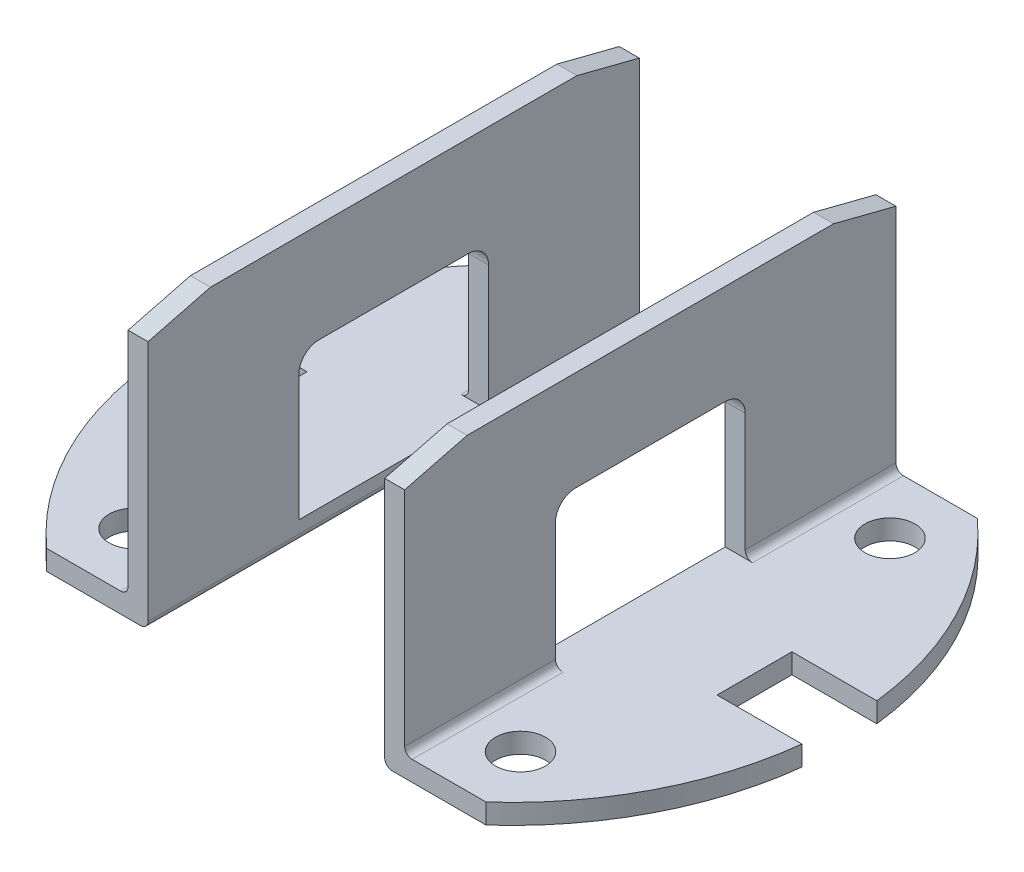
SolidWorks part; units mm, degrees
ref_plane "Front Plane" through (0, 0, 0) normal (0, 0, 1) x (1, 0, 0)
ref_plane "Top Plane" through (0, 0, 0) normal (0, 1, 0) x (1, 0, 0)
ref_plane "Right Plane" through (0, 0, 0) normal (1, 0, 0) x (0, 0, -1)
sketch "Sketch1" plane through (0, 0, 0) normal (0, 1, 0) x (1, 0, 0)
  line L0 (0, 1031.2918) -> (0, -1025.4955) construction
  line L1 (0, 0) -> (-28.6316, 0) construction
  line L2 (11.1742, 12.4968) -> (6.0198, 12.4968)
  line L3 (11.1742, -12.4968) -> (6.0198, -12.4968)
  line L4 (-6.0198, -12.4968) -> (-11.1742, -12.4968)
  line L5 (6.0198, 12.4968) -> (6.0198, -12.4968)
  line L6 (-6.0198, 12.4968) -> (-6.0198, -12.4968)
  line L7 (6.0198, 1031.2918) -> (6.0198, -1025.4955) construction
  line L8 (0, 12.4968) -> (-28.6316, 12.4968) construction
  line L9 (0, -12.4968) -> (-28.6316, -12.4968) construction
  line L10 (-6.0198, 12.4968) -> (-11.1742, 12.4968)
  line L13 (16.6554, 1.905) -> (12.3374, 1.905)
  line L14 (12.3374, 1.905) -> (12.3374, -1.905)
  line L15 (16.6554, -1.905) -> (12.3374, -1.905)
  line L16 (-16.6554, -1.905) -> (-12.3374, -1.905)
  line L18 (-12.3374, 1.905) -> (-12.3374, -1.905)
  line L19 (-16.6554, 1.905) -> (-12.3374, 1.905)
  arc A0 (-11.1742, 12.4968) -> (-16.6554, 1.905) centre (0, 0) ccw
  arc A1 (11.1742, -12.4968) -> (16.6554, -1.905) centre (0, 0) ccw
  arc A2 (-16.6554, -1.905) -> (-11.1742, -12.4968) centre (0, 0) ccw
  arc A4 (16.6554, 1.905) -> (11.1742, 12.4968) centre (0, 0) ccw
  circle A6 centre (-9.8298, 9.398) radius 1.27
  circle A9 centre (-9.8298, -9.398) radius 1.27
  circle A10 centre (9.8298, -9.398) radius 1.27
  circle A11 centre (9.8298, 9.398) radius 1.27
  point P11 (-6.0198, 1031.2918)
  point P12 (-6.0198, -25.4955)
  point P22 (-5.0038, 13.5128)
  point P23 (-5.0038, -13.5128)
  point P24 (-11.5556, -13.5128)
  point P25 (0, 0)
  point P26 (-11.5556, 13.5128)
  point P27 (5.0038, 13.5128)
  point P28 (5.0038, -13.5128)
  point P29 (11.5556, -13.5128)
  point P30 (0, 0)
  point P31 (11.5556, 13.5128)
  point P34 (-10.7792, -11.4808)
  point P35 (0, 0)
  point P36 (-10.7792, 11.4808)
  point P39 (10.7792, -11.4808)
  point P40 (0, 0)
  point P41 (10.7792, 11.4808)
  point P50 (12.3374, 0)
  dimension "D1" = 33.528
  dimension "D8" = 2.54
  dimension "D4" = 1.905
  dimension "D7" = 4.318
  dimension "D9" = 9.398
  dimension "D10" = 3.81
  dimension "D6" = 6.0198
  dimension "D2" = 12.4968
  dimension "D3" = 12.4968
  dimension "D5" = 6.0198
extrude "Boss-Extrude1" add sketch "Sketch1" along normal blind 1.016
sketch "Sketch2" plane through (0, 0, 0) normal (0, 1, 0) x (1, 0, 0)
  line L0 (-6.0198, -12.4968) -> (-6.0198, 12.4968) construction
  line L1 (6.0198, 12.4968) -> (6.0198, -12.4968) construction
  line L2 (-6.0198, -12.4968) -> (-6.0198, 12.4968)
  line L3 (6.0198, 12.4968) -> (6.0198, -12.4968)
  line L4 (-7.0358, -12.4968) -> (-7.0358, 12.4968)
  line L5 (7.0358, 12.4968) -> (7.0358, -12.4968)
  line L6 (-6.0198, 12.4968) -> (-11.1742, 12.4968) construction
  line L7 (-11.1742, -12.4968) -> (-6.0198, -12.4968) construction
  line L8 (6.0198, -12.4968) -> (11.1742, -12.4968) construction
  line L9 (11.1742, 12.4968) -> (6.0198, 12.4968) construction
  line L10 (-6.0198, 12.4968) -> (-7.0358, 12.4968)
  line L11 (-7.0358, -12.4968) -> (-6.0198, -12.4968)
  line L12 (6.0198, -12.4968) -> (7.0358, -12.4968)
  line L13 (7.0358, 12.4968) -> (6.0198, 12.4968)
  dimension "D1" = 1.016
  dimension "D2" = 1.016
extrude "Boss-Extrude2" add sketch "Sketch2" along normal blind 13.5128
sketch "Sketch3" plane through (0, 0, 0) normal (1, 0, 0) x (0, 0, -1)
  line L0 (-12.4968, 13.5128) -> (12.4968, 13.5128) construction
  line L1 (-12.4968, 13.5128) -> (-12.4968, 1.016) construction
  line L2 (12.4968, 13.5128) -> (12.4968, 1.016) construction
  line L3 (-12.4968, 13.5128) -> (-9.3218, 13.5128)
  line L4 (-12.4968, 13.5128) -> (-12.4968, 12.7)
  line L5 (12.4968, 13.5128) -> (12.4968, 12.7)
  line L6 (0, 0) -> (0, 16.3845) construction
  line L7 (9.3218, 13.5128) -> (12.4968, 13.5128)
  line L8 (-9.3218, 13.5128) -> (-12.4968, 12.7)
  line L9 (9.3218, 13.5128) -> (12.4968, 12.7)
  line L10 (-4.826, 7.4168) -> (-4.826, 1.016)
  line L11 (-1.905, 1.016) -> (-12.4968, 1.016) construction
  line L12 (-3.81, 8.4328) -> (3.81, 8.4328)
  line L13 (4.826, 7.4168) -> (4.826, 1.016)
  line L14 (-4.826, 1.016) -> (4.826, 1.016)
  arc A0 (-3.81, 8.4328) -> (-4.826, 7.4168) centre (-3.81, 7.4168) ccw
  arc A1 (3.81, 8.4328) -> (4.826, 7.4168) centre (3.81, 7.4168) cw
  point P22 (0, 8.4328)
  dimension "D4" = 1.016
  dimension "D1" = 4.826
  dimension "D2" = 0.8128
  dimension "D3" = 5.08
extrude "Cut-Extrude1" cut sketch "Sketch3" against normal blind 13.5128 and the other way blind 13.5128
fillet "Fillet1" radius 0.381 3 edges at (-7.0358, 1.016, 8.6614) (-7.0358, 1.016, -8.6614) (-6.0198, 0, 0)
fillet "Fillet2" radius 0.381 3 edges at (7.0358, 1.016, -8.6614) (7.0358, 1.016, 8.6614) (6.0198, 0, 0)
